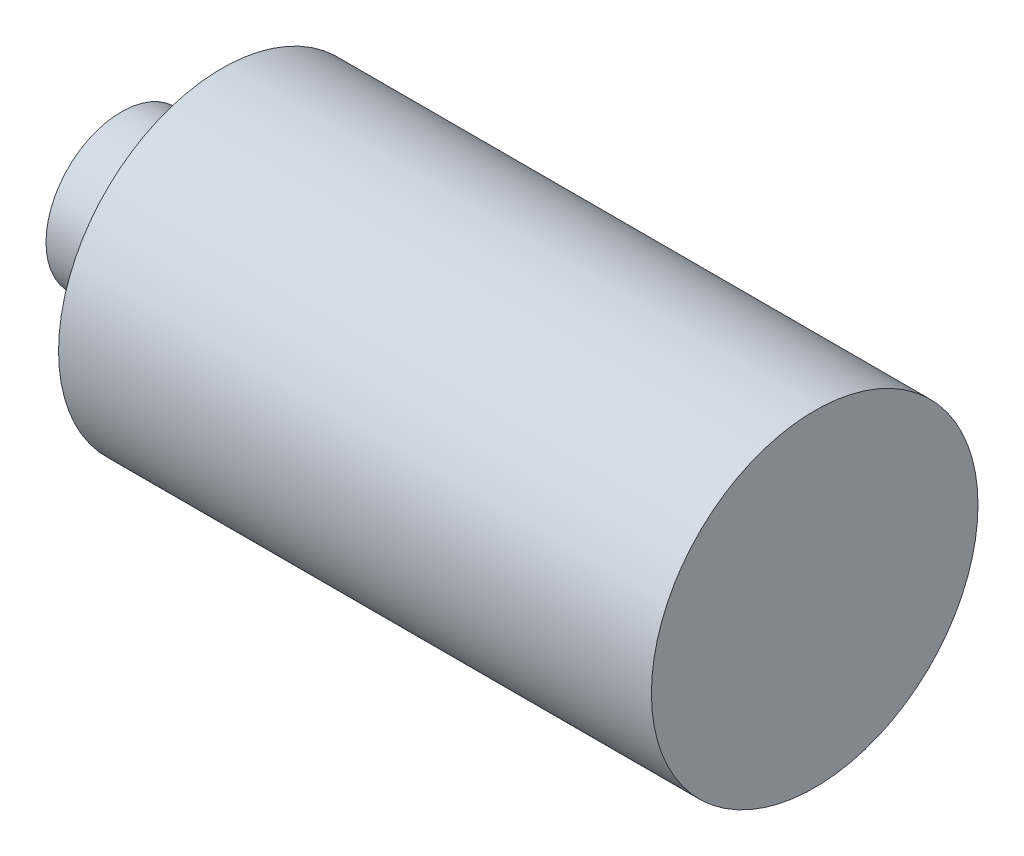
SolidWorks part; units mm, degrees
ref_plane "Front Plane" through (0, 0, 0) normal (0, 0, 1) x (1, 0, 0)
ref_plane "Top Plane" through (0, 0, 0) normal (0, 1, 0) x (1, 0, 0)
ref_plane "Right Plane" through (0, 0, 0) normal (1, 0, 0) x (0, 0, -1)
sketch "Sketch1" plane through (0, 0, 0) normal (0, 0, 1) x (1, 0, 0)
  line L0 (-14.1304, 0) -> (15.8261, 0) construction
  line L1 (11.8, 0) -> (11.8, 3.25)
  line L2 (11.8, 3.25) -> (0, 3.25)
  line L3 (0, 3.25) -> (0, 1.5)
  line L4 (0, 1.5) -> (-2, 1.5)
  line L5 (-2, 1.5) -> (-2, 0)
  line L6 (-2, 0) -> (11.8, 0)
  point P6 (0, 2.375)
  point P10 (-2, 0.75)
  dimension "D1" = 6.5
  dimension "D2" = 3
  dimension "D3" = 2
  dimension "D4" = 11.8
revolve "Revolve1" add sketch "Sketch1" angle 360 about L0
